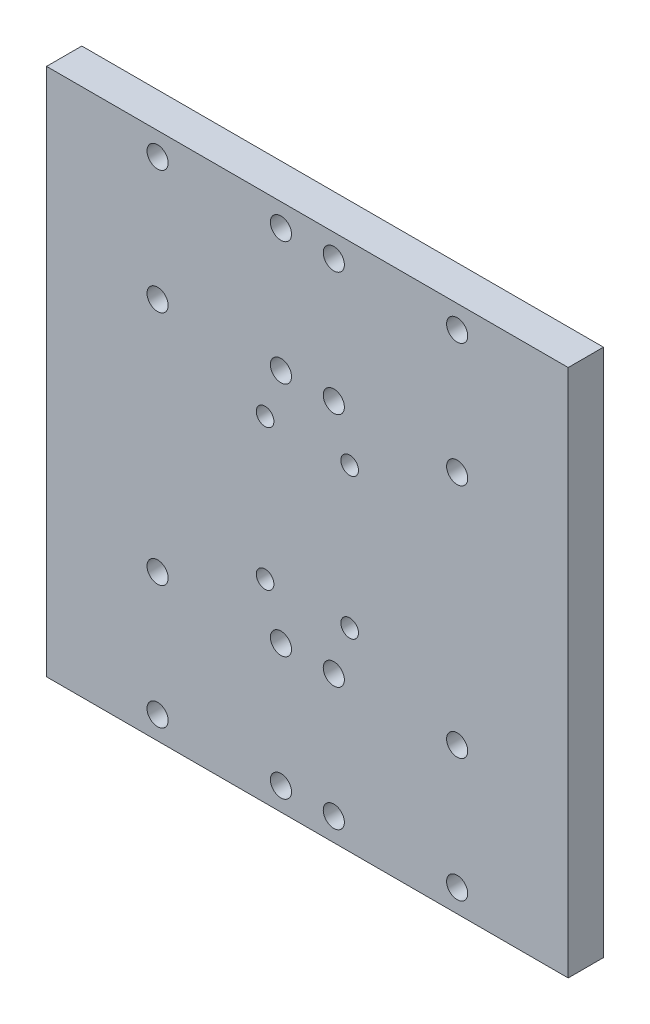
SolidWorks part; units mm, degrees
ref_plane "Front Plane" through (0, 0, 0) normal (0, 0, 1) x (1, 0, 0)
ref_plane "Top Plane" through (0, 0, 0) normal (0, 1, 0) x (1, 0, 0)
ref_plane "Right Plane" through (0, 0, 0) normal (1, 0, 0) x (0, 0, -1)
sketch "Sketch1" plane through (0, 0, 0) normal (0, 0, 1) x (1, 0, 0)
  line L1 (74, -75) -> (-74, -75)
  line L2 (74, -75) -> (74, 75)
  line L3 (74, 75) -> (-74, 75)
  line L4 (-74, -75) -> (-74, 75)
  line L5 (74, -75) -> (-74, 75) construction
  line L6 (74, 75) -> (-74, -75) construction
  point P1 (0, 0)
  dimension "D1" = 148
  dimension "D2" = 150
extrude "Boss-Extrude1" add sketch "Sketch1" along normal blind 10
sketch "Sketch2" plane through (0, 0, 10) normal (0, 0, 1) x (1, 0, 0)
  line L0 (42.5, 0) -> (-46.4389, 0) construction
  line L1 (42.5, 33.5) -> (-42.5, 33.5) construction
  line L2 (42.5, 33.5) -> (42.5, 68.5) construction
  line L3 (42.5, 68.5) -> (-42.5, 68.5) construction
  line L4 (-42.5, 33.5) -> (-42.5, 68.5) construction
  line L5 (42.5, 33.5) -> (-42.5, 68.5) construction
  line L6 (42.5, 68.5) -> (-42.5, 33.5) construction
  line L7 (12, -20) -> (0, 0) construction
  line L8 (0, 0) -> (-12, -20) construction
  line L9 (12, 20) -> (-12, 20) construction
  line L10 (12, -20) -> (-12, -20) construction
  line L11 (0, 0) -> (-12, 20) construction
  line L12 (12, 20) -> (0, 0) construction
  line L13 (42.5, -68.5) -> (-42.5, -33.5) construction
  line L14 (42.5, -33.5) -> (-42.5, -68.5) construction
  line L15 (-42.5, -33.5) -> (-42.5, -68.5) construction
  line L16 (42.5, -68.5) -> (-42.5, -68.5) construction
  line L17 (42.5, -33.5) -> (42.5, -68.5) construction
  line L18 (42.5, -33.5) -> (-42.5, -33.5) construction
  circle A0 centre (-42.5, 68.5) radius 3
  circle A1 centre (-42.5, 33.5) radius 3
  circle A2 centre (42.5, 33.5) radius 3
  circle A3 centre (42.5, 68.5) radius 3
  circle A4 centre (-7.5, 68.5) radius 3
  circle A5 centre (7.5, 68.5) radius 3
  circle A6 centre (-7.5, 33.5) radius 3
  circle A7 centre (7.5, 33.5) radius 3
  circle A8 centre (-12, 20) radius 2.5
  circle A9 centre (12, 20) radius 2.5
  circle A10 centre (12, -20) radius 2.5
  circle A11 centre (-12, -20) radius 2.5
  circle A12 centre (7.5, -33.5) radius 3
  circle A13 centre (-7.5, -33.5) radius 3
  circle A14 centre (7.5, -68.5) radius 3
  circle A15 centre (-7.5, -68.5) radius 3
  circle A16 centre (42.5, -68.5) radius 3
  circle A17 centre (42.5, -33.5) radius 3
  circle A18 centre (-42.5, -33.5) radius 3
  circle A19 centre (-42.5, -68.5) radius 3
  point P0 (0, 51)
  point P5 (0, 0)
  point P46 (0, -51)
  dimension "D1" = 6
  dimension "D8" = 5
  dimension "D2" = 85
  dimension "D3" = 35
  dimension "D4" = 35
  dimension "D5" = 51
  dimension "D6" = 24
  dimension "D7" = 20
  dimension "D9" = 35
extrude "Cut-Extrude1" cut sketch "Sketch2" against normal through all
